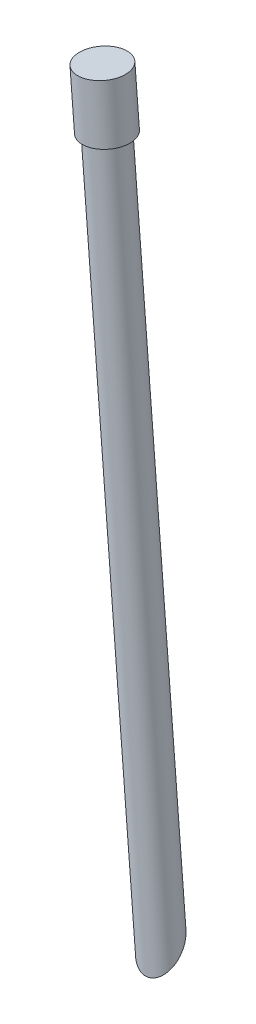
SolidWorks part; units mm, degrees
ref_plane "前视基准面" through (0, 0, 0) normal (0, 0, 1) x (1, 0, 0)
ref_plane "上视基准面" through (0, 0, 0) normal (0, 1, 0) x (1, 0, 0)
ref_plane "右视基准面" through (0, 0, 0) normal (1, 0, 0) x (0, 0, -1)
sketch "草图1" plane through (0, 0, 0) normal (0, 0, 1) x (1, 0, 0)
  line L0 (2.315, 264.6208) -> (8.3762, 188.527) construction
  line L1 (3.0502, 255.3907) -> (5.0314, 255.5485)
  line L2 (5.0314, 255.5485) -> (5.4253, 250.6031)
  line L3 (5.4253, 250.6031) -> (5.0261, 250.6031)
  line L4 (5.0261, 250.6031) -> (9.9607, 188.6532)
  line L5 (9.9607, 188.6532) -> (8.3762, 188.527)
  line L6 (8.3762, 188.527) -> (3.0502, 255.3907)
revolve "旋转1" add sketch "草图1" angle 360 about L0
sketch "草图2" plane through (0, 0, 0) normal (1, 0, 0) x (0, 0, -1)
  line L0 (47.2909, 235.0024) -> (47.2909, 71.8809) construction
  line L1 (47.2909, 71.8809) -> (47.2909, 211.2796)
  arc A0 (47.2909, 211.2796) -> (47.2909, 71.8809) centre (47.2909, 141.5803) ccw
revolve "切除-旋转1" cut sketch "草图2" angle 360 about L0
